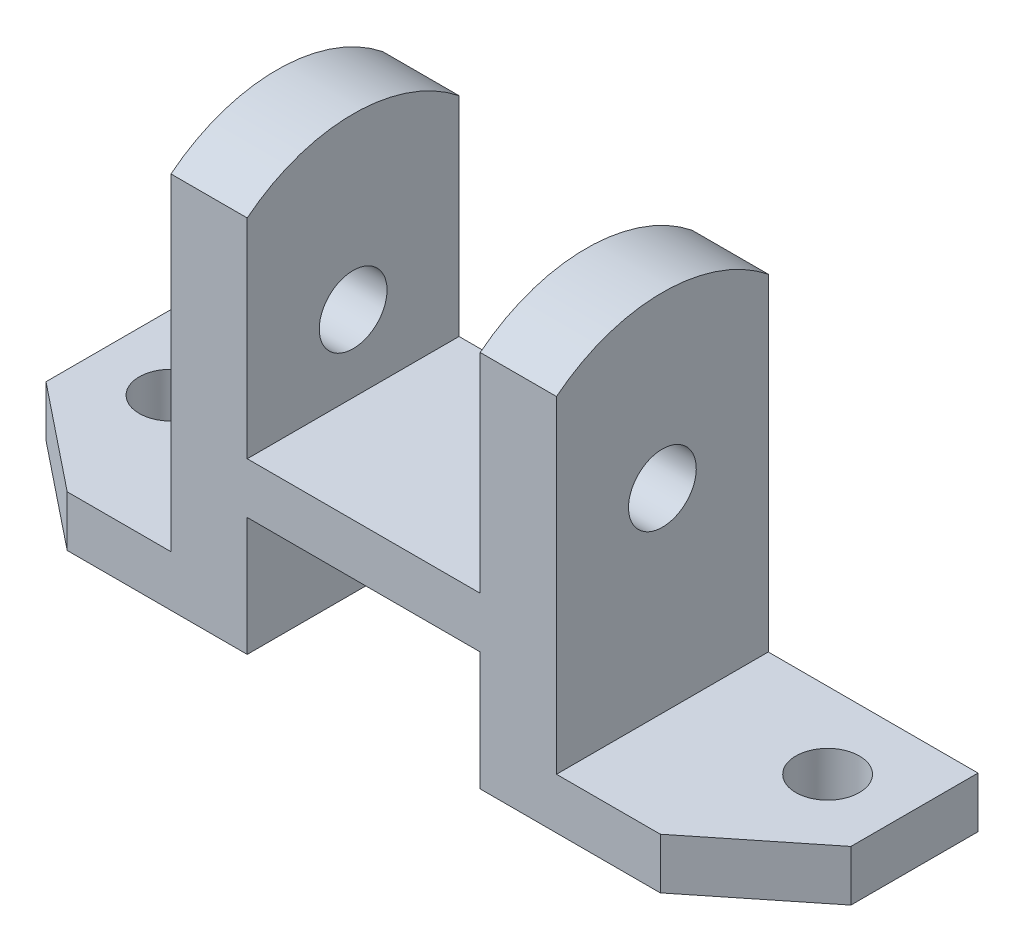
SolidWorks part; units mm, degrees
ref_plane "Front Plane" through (0, 0, 0) normal (0, 0, 1) x (1, 0, 0)
ref_plane "Top Plane" through (0, 0, 0) normal (0, 1, 0) x (1, 0, 0)
ref_plane "Right Plane" through (0, 0, 0) normal (1, 0, 0) x (0, 0, -1)
sketch "Sketch1" plane through (0, 0, 0) normal (0, 1, 0) x (1, 0, 0)
  line L0 (-95, -5) -> (-70, -25)
  line L1 (-95, -25) -> (95, -25)
  line L2 (-95, -25) -> (-95, 25)
  line L3 (-95, 25) -> (95, 25)
  line L4 (95, -25) -> (95, 25)
  line L5 (-95, -25) -> (95, 25) construction
  line L6 (-95, 25) -> (95, -25) construction
  line L7 (0, 25) -> (0, -45.0109) construction
  line L8 (95, -5) -> (70, -25)
  circle A0 centre (-77.5, 7) radius 7.5
  circle A1 centre (77.5, 7) radius 7.5
  point P0 (0, 0)
  dimension "D6" = 15
  dimension "D7" = 155
  dimension "D1" = 190
  dimension "D2" = 50
  dimension "D3" = 20
  dimension "D4" = 25
  dimension "D5" = 18
extrude "Boss-Extrude1" add sketch "Sketch1" along normal blind 98 contours L8 L4 L3 L2 L0 L1 A0 A1
sketch "Sketch2" plane through (0, 0, 25) normal (0, 0, 1) x (1, 0, 0)
  line L0 (0, 98) -> (0, -2.0273) construction
  line L1 (-70, 98) -> (70, 98) construction
  line L2 (-70, 0) -> (70, 0) construction
  line L3 (-95, 98) -> (-45.5, 98)
  line L4 (-95, 98) -> (-95, 12)
  line L5 (-95, 12) -> (-45.5, 12)
  line L6 (-45.5, 98) -> (-45.5, 12)
  line L7 (95, 12) -> (45.5, 12)
  line L8 (-27.5, 98) -> (27.5, 98)
  line L9 (-27.5, 98) -> (-27.5, 40)
  line L10 (-27.5, 40) -> (27.5, 40)
  line L11 (27.5, 98) -> (27.5, 40)
  line L12 (95, 98) -> (45.5, 98)
  line L13 (95, 98) -> (95, 12)
  line L14 (45.5, 98) -> (45.5, 12)
  dimension "D1" = 12
  dimension "D2" = 55
  dimension "D3" = 18
  dimension "D4" = 58
extrude "Cut-Extrude1" cut sketch "Sketch2" against normal through all
sketch "Sketch3" plane through (0, 0, 25) normal (0, 0, 1) x (1, 0, 0)
  line L0 (-70, 0) -> (70, 0) construction
  line L1 (-27.5, 0) -> (27.5, 0)
  line L2 (-27.5, 0) -> (-27.5, 28)
  line L3 (-27.5, 28) -> (27.5, 28)
  line L4 (27.5, 0) -> (27.5, 28)
  line L5 (0, 0) -> (0, 53.4547) construction
  line L6 (-27.5, 98) -> (-27.5, 40) construction
  line L7 (-27.5, 40) -> (27.5, 40) construction
  dimension "D1" = 12
extrude "Cut-Extrude2" cut sketch "Sketch3" against normal through all contours L2 L1 L4 L3
sketch "Sketch4" plane through (0, 28, 0) normal (0, -1, 0) x (1, 0, 0)
  line L0 (77.5, -7) -> (-77.5, -7) construction
  line L1 (27.5, -25) -> (27.5, 25) construction
  line L2 (-27.5, -3) -> (27.5, -3)
  line L3 (-27.5, -3) -> (-27.5, -11)
  line L4 (-27.5, -11) -> (27.5, -11)
  line L5 (27.5, -3) -> (27.5, -11)
  line L6 (-27.5, -3) -> (27.5, -11) construction
  line L7 (-27.5, -11) -> (27.5, -3) construction
  point P4 (0, -7)
  dimension "D1" = 8
extrude "Boss-Extrude2" add sketch "Sketch4" along normal up to surface (28 mm away) up to face at (-77.5, 0, 0.5)
sketch "Sketch5" plane through (45.5, 0, 0) normal (1, 0, 0) x (0, 0, -1)
  line L2 (25, 89.225) -> (25, 98)
  line L5 (-25, 98) -> (-25, 12)
  line L6 (-25, 12) -> (25, 12)
  line L7 (25, 12) -> (25, 98)
  line L8 (25, 98) -> (-25, 98)
  line L9 (-25, 98) -> (-25, 89.225)
  line L12 (25, 98) -> (-25, 98)
  circle A0 centre (0, 58) radius 8
  arc A2 (25, 89.225) -> (-25, 89.225) centre (0, 58) ccw
  line M5 (-25, 98) -> (-25, 12)
  line M7 (25, 12) -> (25, 98)
  line M8 (25, 98) -> (-25, 98)
  dimension "D1" = 16
  dimension "D3" = 0
extrude "Cut-Extrude3" cut sketch "Sketch5" against normal through all contours A2 M7 M8 | A2 L12 M5 | A0
